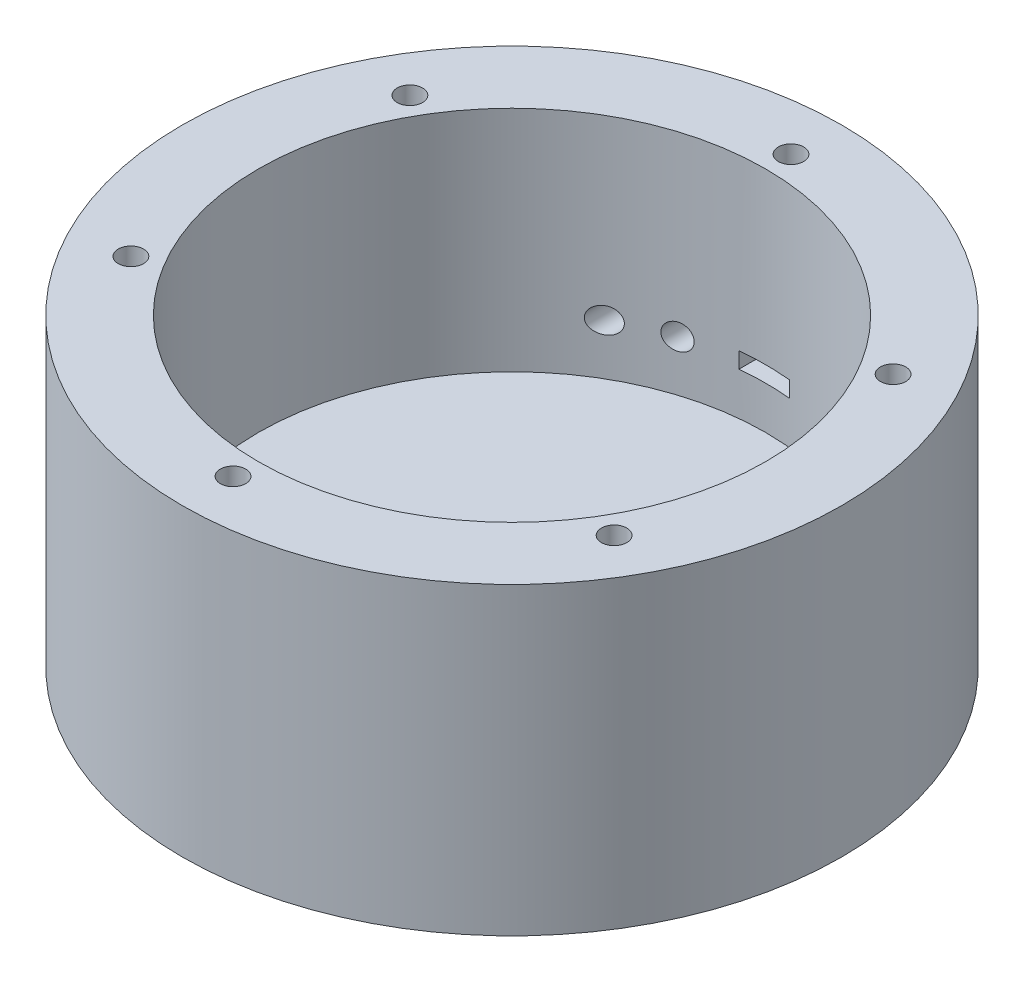
SolidWorks part; units mm, degrees
ref_plane "Alzado" through (0, 0, 0) normal (0, 0, 1) x (1, 0, 0)
ref_plane "Planta" through (0, 0, 0) normal (0, 1, 0) x (1, 0, 0)
ref_plane "Vista lateral" through (0, 0, 0) normal (1, 0, 0) x (0, 0, -1)
sketch "Croquis1" plane through (0, 0, 0) normal (0, 1, 0) x (1, 0, 0)
  circle A0 centre (0, 0) radius 65
  dimension "D1" = 130
extrude "Saliente-Extruir1" add sketch "Croquis1" along normal blind 60
shell "Vaciado1" thickness 15
sketch "Croquis3" plane through (0, 60, 0) normal (0, 1, 0) x (1, 0, 0)
  circle A0 centre (0, 55) radius 2.5
  circle A1 centre (0, 0) radius 65 construction
  circle A2 centre (47.6314, 27.5) radius 2.5
  circle A3 centre (47.6314, -27.5) radius 2.5
  circle A4 centre (0, -55) radius 2.5
  circle A5 centre (-47.6314, -27.5) radius 2.5
  circle A6 centre (-47.6314, 27.5) radius 2.5
  point P18 (0, 0)
  dimension "D1" = 5
  dimension "D2" = 55
  dimension "D4" = 27.5
  dimension "D5" = 47.6314
  dimension "D3" = 6
extrude "Cortar-Extruir1" cut sketch "Croquis3" against normal blind 10
sketch "Croquis4" plane through (6.13, -2.1034, -123.9923) normal (0, 0, 1) x (1, 0, 0)
  line L1 (-11.13, 28.6784) -> (-1.13, 28.6784)
  line L2 (-11.13, 28.6784) -> (-11.13, 25.5284)
  line L3 (-11.13, 25.5284) -> (-1.13, 25.5284)
  line L4 (-1.13, 28.6784) -> (-1.13, 25.5284)
  line L5 (-11.13, 28.6784) -> (-1.13, 25.5284) construction
  line L6 (-11.13, 25.5284) -> (-1.13, 28.6784) construction
  circle A0 centre (-21.13, 27.1034) radius 2.5
  circle A1 centre (-31.13, 27.1034) radius 2.5
  point P0 (-6.13, 27.1034)
  dimension "D4" = 5
  dimension "D5" = 15
  dimension "D1" = 10
  dimension "D2" = 3.15
  dimension "D3" = 25
  dimension "D6" = 10
extrude "Cortar-Extruir2" cut sketch "Croquis4" along normal up to surface (74.243 mm away)
sketch "Croquis5" plane through (6.13, -2.1034, -123.9923) normal (1, 0, 0) x (0, 0, -1)
